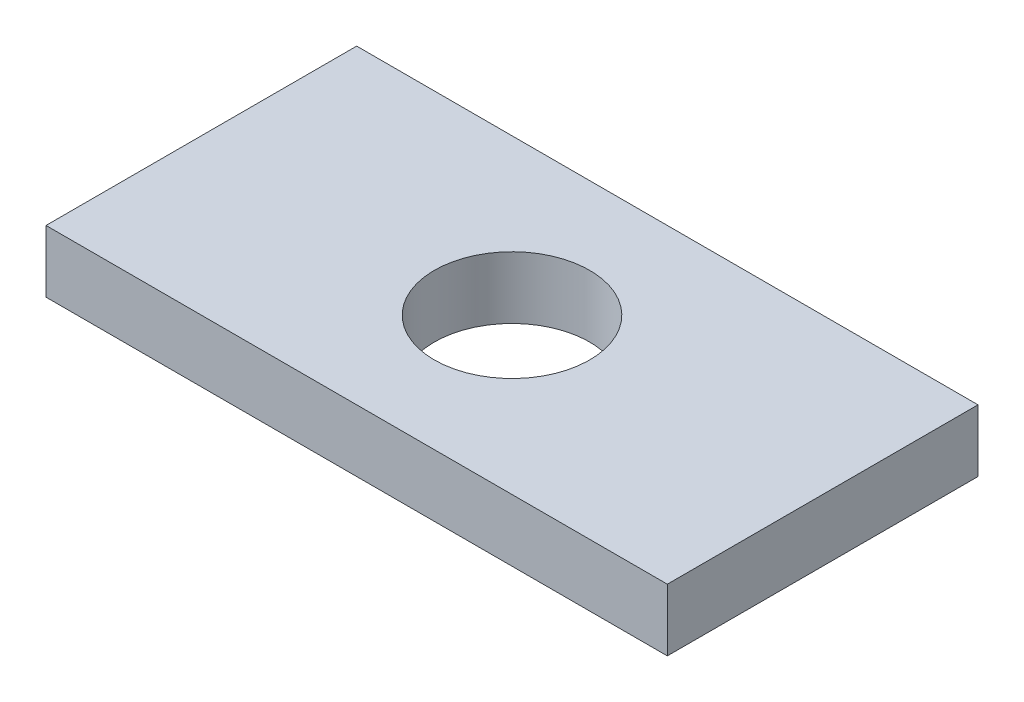
SolidWorks part; units mm, degrees
ref_plane "Спереди" through (0, 0, 0) normal (0, 0, 1) x (1, 0, 0)
ref_plane "Сверху" through (0, 0, 0) normal (0, 1, 0) x (1, 0, 0)
ref_plane "Справа" through (0, 0, 0) normal (1, 0, 0) x (0, 0, -1)
sketch "Эскиз1" plane through (0, 0, 0) normal (0, 1, 0) x (1, 0, 0)
  line L1 (0, 0) -> (40, 0)
  line L2 (0, 0) -> (0, 20)
  line L3 (0, 20) -> (40, 20)
  line L4 (40, 0) -> (40, 20)
extrude "Бобышка-Вытянуть1" add sketch "Эскиз1" along normal blind 4
sketch "Эскиз2" plane through (0, 4, 0) normal (0, 1, 0) x (1, 0, 0)
  circle A0 centre (20, 10) radius 5
extrude "Вырез-Вытянуть1" cut sketch "Эскиз2" against normal through all
